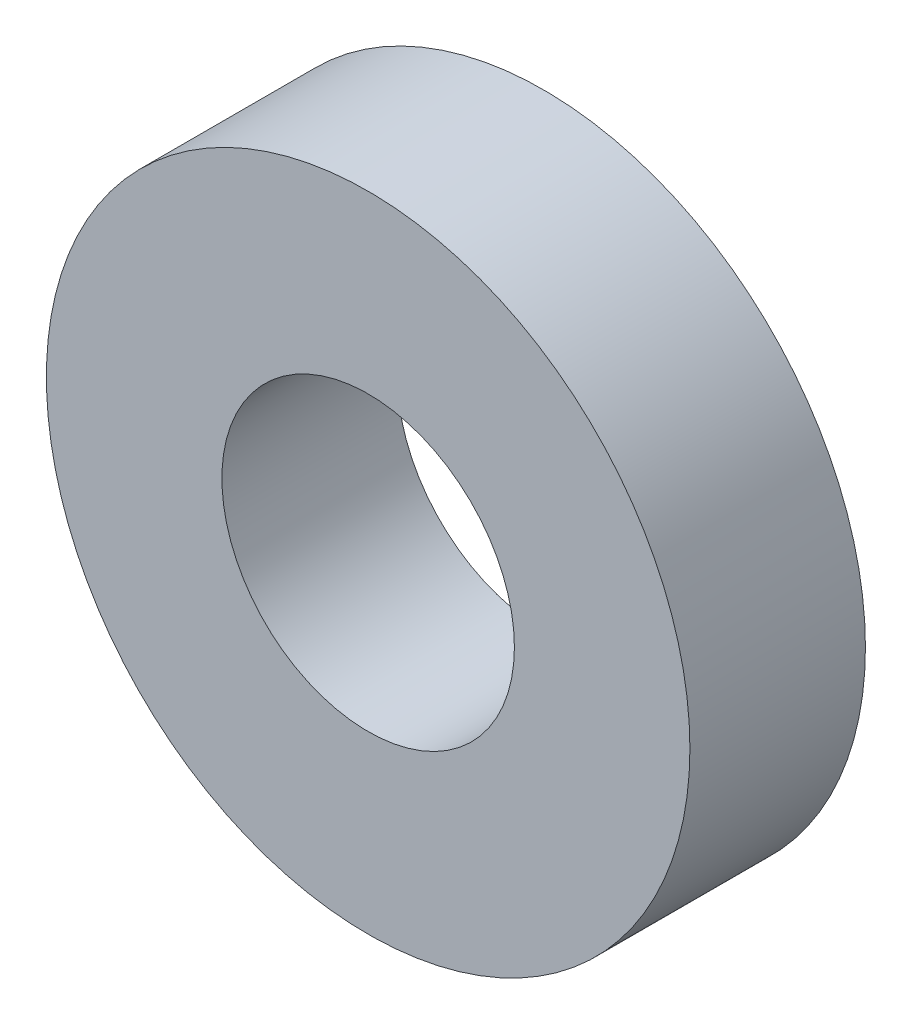
SolidWorks part; units mm, degrees
material "BUTYL"
ref_plane "Plan de face" through (0, 0, 0) normal (0, 0, 1) x (1, 0, 0)
ref_plane "Plan de dessus" through (0, 0, 0) normal (0, 1, 0) x (1, 0, 0)
ref_plane "Plan de droite" through (0, 0, 0) normal (1, 0, 0) x (0, 0, -1)
sketch "Esquisse1" plane through (0, 0, 0) normal (0, 0, 1) x (1, 0, 0)
  circle A0 centre (0, 0) radius 2.5
  circle A1 centre (0, 0) radius 5.5
  dimension "D1" = 5
  dimension "D2" = 3
extrude "Boss.-Extru.1" add sketch "Esquisse1" along normal blind 3
